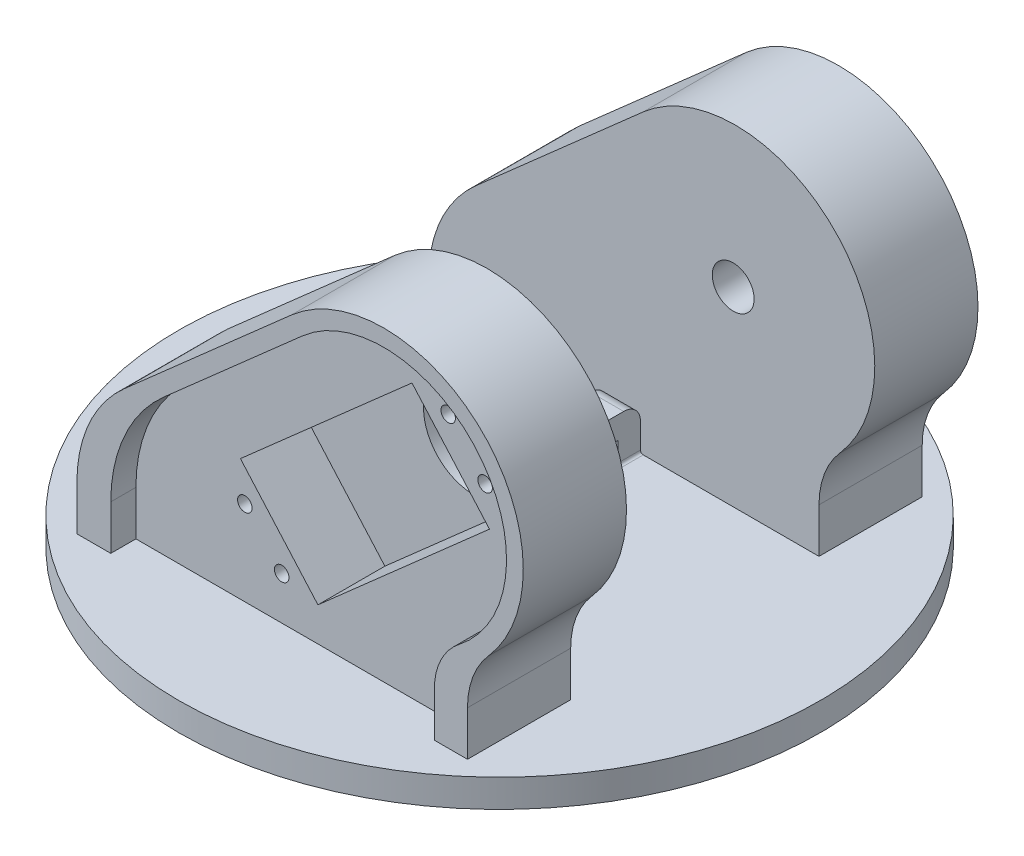
SolidWorks part; units mm, degrees
ref_plane "Front Plane" through (0, 0, 0) normal (0, 0, 1) x (1, 0, 0)
ref_plane "Top Plane" through (0, 0, 0) normal (0, 1, 0) x (1, 0, 0)
ref_plane "Right Plane" through (0, 0, 0) normal (1, 0, 0) x (0, 0, -1)
sketch "Sketch1" plane through (0, 0, 0) normal (0, 1, 0) x (1, 0, 0)
  circle A0 centre (0, 0) radius 57.5
  dimension "D1" = 115
extrude "Boss-Extrude1" add sketch "Sketch1" along normal blind 5 contours A0
sketch "Sketch2" plane through (0, 0, 0) normal (0, 0, 1) x (1, 0, 0)
  line L0 (-35, 5) -> (-35, 13)
  line L1 (57.5, 5) -> (-57.5, 5) construction
  line L2 (-26.5359, 31.75) -> (3.4641, 58.2075)
  line L3 (35, 13) -> (35, 5)
  line L4 (35, 5) -> (-35, 5)
  arc A0 (-35, 13) -> (-26.5359, 31.75) centre (-10, 13) cw
  arc A1 (3.4641, 58.2075) -> (38.75, 22.9216) centre (20, 39.4575) cw
  arc A2 (38.75, 22.9216) -> (35, 13) centre (50, 13) ccw
  dimension "D2" = 25
  dimension "D4" = 25
  dimension "D5" = 15
  dimension "D1" = 8
  dimension "D3" = 40
  dimension "D6" = 70
  dimension "D7" = 35
extrude "Boss-Extrude2" add sketch "Sketch2" along normal mid plane 81.5
sketch "Sketch4" plane through (0, 0, 0) normal (0, 0, 1) x (1, 0, 0)
  line L0 (3.4641, 58.2075) -> (-26.5359, 31.75) construction
  line L1 (3.4641, 58.2075) -> (-26.5359, 31.75)
  line L3 (-35, 13) -> (-35, 5)
  line L4 (-35, 5) -> (35, 5)
  line L5 (35, 5) -> (35, 13)
  arc A0 (38.75, 22.9216) -> (35, 13) centre (50, 13) ccw construction
  arc A1 (38.75, 22.9216) -> (3.4641, 58.2075) centre (20, 39.4575) ccw construction
  arc A2 (-26.5359, 31.75) -> (-35, 13) centre (-10, 13) ccw construction
  arc A3 (38.75, 22.9216) -> (35, 13) centre (50, 13) ccw
  arc A4 (38.75, 22.9216) -> (3.4641, 58.2075) centre (20, 39.4575) ccw
  arc A5 (-26.5359, 31.75) -> (-35, 13) centre (-10, 13) ccw
extrude "Cut-Extrude1" cut sketch "Sketch4" against normal mid plane 44.5
sketch "Sketch5" plane through (0, 0, 40.75) normal (0, 0, 1) x (1, 0, 0)
  line L0 (5.4484, 55.9575) -> (-19.4491, 34)
  line L1 (-28.9289, 13) -> (-28.9289, 5)
  line L2 (-35, 5) -> (35, 5) construction
  line L4 (29.0711, 13) -> (29.0711, 5)
  line L5 (29.0711, 5) -> (-28.9289, 5)
  line L6 (3.4641, 58.2075) -> (-26.5359, 31.75) construction
  arc A0 (-19.4491, 34) -> (-28.9289, 13) centre (-0.9289, 13) ccw
  arc A1 (33.5184, 22.1009) -> (5.4484, 55.9575) centre (20, 39.4575) ccw
  arc A2 (33.5184, 22.1009) -> (29.0711, 13) centre (40.6068, 13) ccw
  arc A3 (38.75, 22.9216) -> (3.4641, 58.2075) centre (20, 39.4575) ccw construction
  dimension "D1" = 22
  dimension "D2" = 28
  dimension "D3" = 58
extrude "Cut-Extrude2" cut sketch "Sketch5" against normal blind 4.5
mirror "Mirror1" about plane through (0, 0, 0) normal (0, 0, 1) of "Cut-Extrude2"
sketch "Sketch6" plane through (0, 0, 36.25) normal (0, 0, 1) x (1, 0, 0)
  line L0 (20.5549, 53.9469) -> (-10.1951, 26.8279)
  line L1 (-10.1951, 26.8279) -> (3.6951, 11.0779)
  line L2 (20.5549, 53.9469) -> (34.4451, 38.1969)
  line L3 (34.4451, 38.1969) -> (3.6951, 11.0779)
  line L5 (5.4484, 55.9575) -> (-19.4491, 34) construction
  arc A0 (33.5184, 22.1009) -> (5.4484, 55.9575) centre (20, 39.4575) ccw construction
  dimension "D1" = 41
  dimension "D2" = 21
  dimension "D3" = 11.5
  dimension "D4" = 10
extrude "Cut-Extrude3" cut sketch "Sketch6" against normal blind 12
sketch "Sketch7" plane through (0, 0, 24.25) normal (0, 0, 1) x (1, 0, 0)
  line L0 (34.4451, 38.1969) -> (20.5549, 53.9469) construction
  line L1 (20.5549, 53.9469) -> (-10.1951, 26.8279) construction
  circle A0 centre (19.625, 39.1268) radius 9
  dimension "D1" = 18
  dimension "D2" = 10.5
  dimension "D3" = 10.5
extrude "Cut-Extrude5" cut sketch "Sketch7" against normal up to surface (2 mm away) up to face at (4.1892, 23.8147, 22.25)
sketch "Sketch8" plane through (0, 0, 36.25) normal (0, 0, 1) x (1, 0, 0)
  line L0 (34.4451, 38.1969) -> (20.5549, 53.9469) construction
  line L1 (-10.1951, 26.8279) -> (3.6951, 11.0779) construction
  line L2 (27.5, 46.0719) -> (36.5, 54.0091) construction
  line L3 (-3.25, 18.9529) -> (-19.0711, 5) construction
  line L4 (-10.1951, 26.8279) -> (3.6951, 11.0779) construction
  line L5 (-28.9289, 5) -> (29.0711, 5) construction
  line L6 (-28.9289, 13) -> (-28.9289, 5) construction
  circle A0 centre (27.0428, 52.3354) radius 1.3
  circle A1 centre (33.6572, 44.8354) radius 1.3
  circle A2 centre (-9.4072, 20.1895) radius 1.3
  circle A3 centre (-2.7928, 12.6895) radius 1.3
  arc A4 (33.5184, 22.1009) -> (5.4484, 55.9575) centre (20, 39.4575) ccw construction
  dimension "D1" = 2.6
  dimension "D2" = 3.8
  dimension "D3" = 3.8
  dimension "D4" = 3.8
  dimension "D5" = 10
  dimension "D6" = 10
  dimension "D7" = 9.8577
extrude "Cut-Extrude6" cut sketch "Sketch8" against normal blind 7.5
sketch "Sketch10" plane through (0, 0, -22.25) normal (0, 0, 1) x (1, 0, 0)
  circle A0 centre (19.625, 39.1268) radius 3.75
  dimension "D1" = 7.5
extrude "Cut-Extrude7" cut sketch "Sketch10" against normal up to surface (14 mm away) up to face at (4.8489, 23.4375, -36.25)
sketch "Sketch11" plane through (0, 0, 0) normal (0, -1, 0) x (1, 0, 0)
  circle A0 centre (0, 0) radius 3.75
  dimension "D1" = 7.5
extrude "Cut-Extrude8" cut sketch "Sketch11" against normal blind 2
sketch "Sketch12" plane through (0, 0, 0) normal (0, -1, 0) x (1, 0, 0)
  circle A0 centre (7, 0) radius 0.85
  circle A1 centre (-7, 0) radius 0.85
  circle A2 centre (0, 0) radius 3.75 construction
  dimension "D1" = 1.7
  dimension "D2" = 7
  dimension "D3" = 7
extrude "Cut-Extrude9" cut sketch "Sketch12" against normal up to next
sketch "Sketch13" plane through (0, 0, 0) normal (1, 0, 0) x (0, 0, -1)
  line L0 (22.25, 5) -> (22.25, 10)
  line L1 (22.25, 22.9216) -> (22.25, 13) construction
  line L2 (19.25, 13) -> (9.25, 13)
  line L3 (6.25, 10) -> (6.25, 5)
  line L4 (57.5, 5) -> (-57.5, 5) construction
  line L6 (10.25, 9) -> (18.25, 9)
  line L7 (18.25, 9) -> (18.25, 5)
  line L9 (10.25, 5) -> (10.25, 9)
  line L10 (10.25, 5) -> (6.25, 5)
  line L11 (18.25, 5) -> (22.25, 5)
  arc A0 (22.25, 10) -> (19.25, 13) centre (19.25, 10) ccw
  arc A1 (9.25, 13) -> (6.25, 10) centre (9.25, 10) ccw
  point P15 (14.25, 9)
  point P18 (14.25, 13)
  dimension "D5" = 3
  dimension "D2" = 16
  dimension "D3" = 8
  dimension "D4" = 4
  dimension "D6" = 4
extrude "Boss-Extrude3" add sketch "Sketch13" along normal mid plane 6
fillet "Fillet1" radius 0.5 7 edges at (0, 5, -6.25) (0, 5, -10.25) (3, 5, -8.25) (-3, 5, -8.25) (-3, 5, -20.25) (0, 5, -18.25) (3, 5, -20.25)
